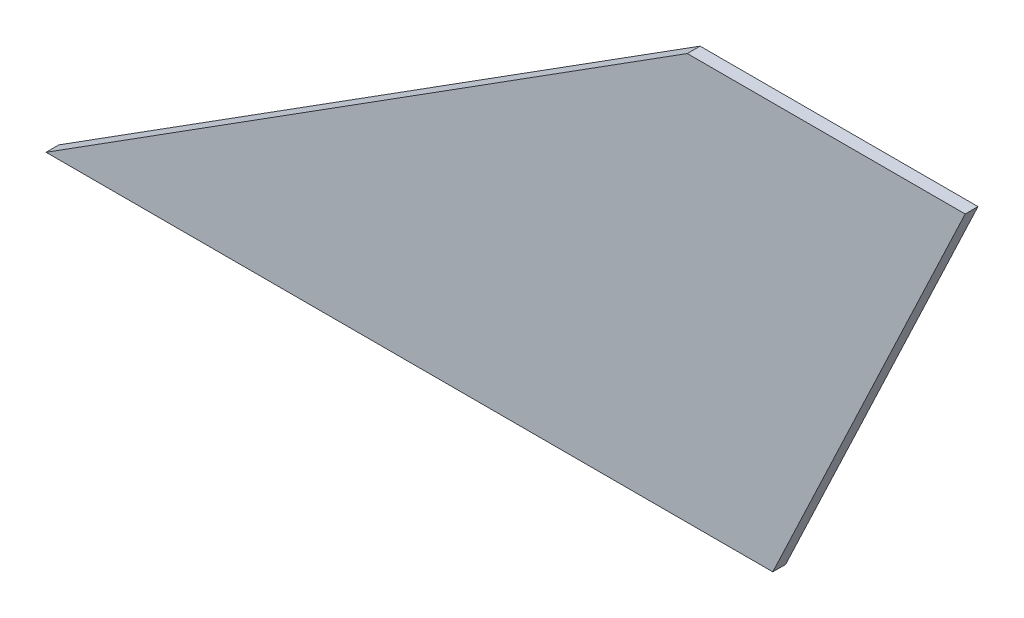
SolidWorks part; units mm, degrees
ref_plane "Front Plane" through (0, 0, 0) normal (0, 0, 1) x (1, 0, 0)
ref_plane "Top Plane" through (0, 0, 0) normal (0, 1, 0) x (1, 0, 0)
ref_plane "Right Plane" through (0, 0, 0) normal (1, 0, 0) x (0, 0, -1)
sketch "Sketch1" plane through (0, 0, 0) normal (0, 0, 1) x (1, 0, 0)
  line L0 (0, 0) -> (170, 0)
  line L1 (170, 0) -> (215, 95)
  line L2 (215, 95) -> (150, 95)
  line L3 (150, 95) -> (0, 0)
  point P6 (0, 2.2854)
  dimension "D1" = 170
  dimension "D2" = 65
  dimension "D3" = 95
  dimension "D4" = 150
extrude "Boss-Extrude1" add sketch "Sketch1" along normal blind 3
